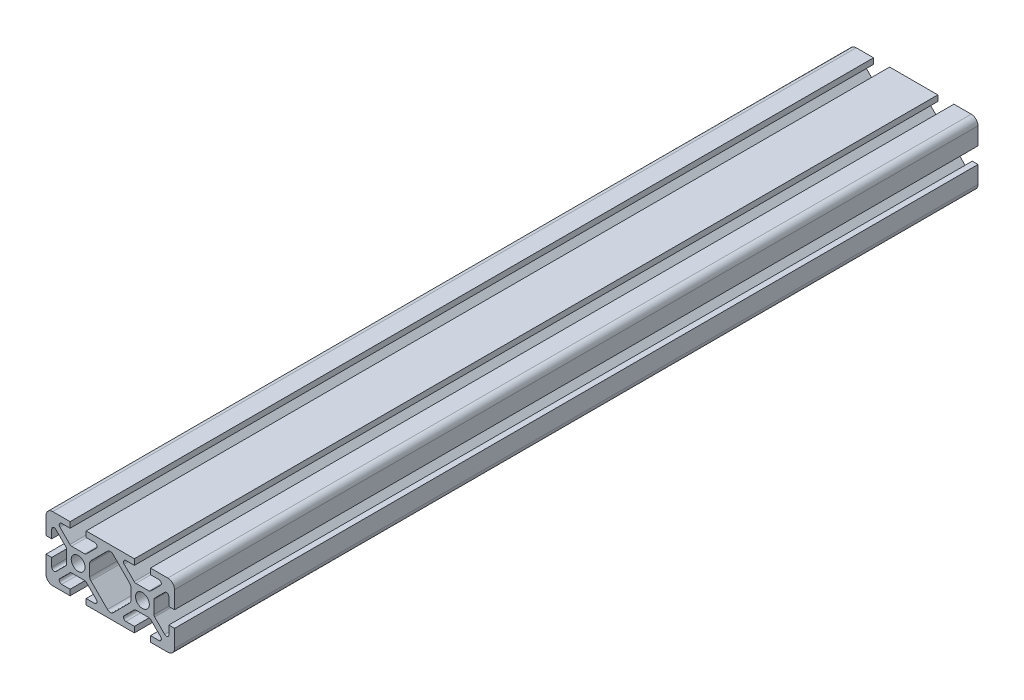
SolidWorks part; units mm, degrees
ref_plane "Front Plane" through (0, 0, 0) normal (0, 0, 1) x (1, 0, 0)
ref_plane "Top Plane" through (0, 0, 0) normal (0, 1, 0) x (1, 0, 0)
ref_plane "Right Plane" through (0, 0, 0) normal (1, 0, 0) x (0, 0, -1)
sketch "Sketch1" plane through (0, 0, 0) normal (0, 0, 1) x (1, 0, 0)
  line L0 (10, 10) -> (10, -10) construction
  line L1 (-20, 0) -> (20, 0) construction
  line L2 (12.5, -10) -> (20, -10)
  line L3 (20, -10) -> (20, -2.5)
  line L4 (12.5, -10) -> (12.5, -8.2134)
  line L5 (12.5, -8.2134) -> (16.95, -8.2134)
  line L6 (16.95, -8.2134) -> (12.3366, -3.6)
  line L7 (10, 0) -> (20, -10) construction
  line L8 (20, -2.5) -> (18.2134, -2.5)
  line L9 (18.2134, -2.5) -> (18.2134, -6.95)
  line L10 (18.2134, -6.95) -> (13.6, -2.3366)
  line L11 (15.9067, -4.6433) -> (14.6433, -5.9067) construction
  line L12 (0, 10) -> (0, -10) construction
  line L13 (0, -10) -> (-20, -10) construction
  line L14 (-10, 10) -> (10, 10) construction
  line L15 (20, 2.5) -> (20, -2.5) construction
  circle A0 centre (10, 0) radius 2.15
  arc A1 (15.5015, -8.2134) -> (15.9257, -7.1891) centre (15.5015, -7.6134) ccw construction
  point P8 (10, -3.6)
  point P16 (15.275, -5.275)
  point P30 (20, 0)
  dimension "Center Hole Diameter" = 4.3
  dimension "D3" = 0.6
  dimension "Rail Width" = 20
  dimension "T-Slot Width" = 5
  dimension "Slot Depth" = 6.4
  dimension "Rail Height" = 40
  dimension "Inner Slot Width" = 13.9
  dimension "Hole Spacing" = 20
sketch "Sketch2" plane through (0, 0, 0) normal (1, 0, 0) x (0, 0, -1)
  line L0 (-125, -10) -> (125, -10) construction
  line L1 (-85, 0) -> (85, 0) construction
  point P6 (-85, 0)
  point P8 (85, 0)
  dimension "Length" = 250
  dimension "D1" = 40
sketch "Sketch3" plane through (0, 0, 0) normal (0, 0, 1) x (1, 0, 0)
  line L0 (12.5, -10) -> (17.9, -10)
  line L1 (12.5, -10) -> (20, -10) construction
  line L2 (12.5, -10) -> (12.5, -8.2134) construction
  line L3 (12.5, -8.2134) -> (16.95, -8.2134) construction
  line L4 (12.5, -8.2134) -> (12.5, -10)
  line L5 (12.5, -8.2134) -> (16.95, -8.2134)
  line L6 (10, -3.6) -> (12.3366, -3.6)
  line L7 (16.95, -8.2134) -> (12.3366, -3.6) construction
  line L8 (12.3366, -3.6) -> (16.95, -8.2134)
  line L9 (20, -10) -> (20, -2.5) construction
  line L10 (18.2134, -6.95) -> (13.6, -2.3366) construction
  line L11 (18.2134, -2.5) -> (18.2134, -6.95) construction
  line L12 (18.2134, -6.95) -> (18.2134, -2.5)
  line L13 (20, -2.5) -> (18.2134, -2.5) construction
  line L14 (18.2134, -2.5) -> (20, -2.5)
  line L15 (20, -2.5) -> (20, -7.9)
  line L16 (18.2134, -6.95) -> (13.6, -2.3366)
  line L17 (13.6, 0) -> (13.6, -2.3366)
  line L18 (-20, 0) -> (20, 0) construction
  line L19 (10, -3.6) -> (10, -2.15)
  line L20 (10, 10) -> (10, -10) construction
  line L21 (13.6, 0) -> (12.15, 0)
  arc A5 (17.9, -10) -> (20, -7.9) centre (17.9, -7.9) ccw
  circle A10 centre (10, 0) radius 2.15 construction
  arc A11 (10, -2.15) -> (12.15, 0) centre (10, 0) ccw
  dimension "D1" = 2.1
extrude "Boss-Extrude1" add sketch "Sketch3" along normal mid plane 250
sketch "Sketch4" plane through (0, 0, 0) normal (0, 0, 1) x (1, 0, 0)
  line L0 (10, -3.6) -> (7.6634, -3.6)
  line L4 (7.6634, -3.6) -> (3.05, -8.2134)
  line L5 (3.05, -8.2134) -> (7.5, -8.2134)
  line L6 (7.5, -8.2134) -> (7.5, -10)
  line L18 (7.5, -10) -> (0, -10)
  line L19 (12.5, -10) -> (12.5, -8.2134) construction
  line L20 (12.5, -8.2134) -> (16.95, -8.2134) construction
  line L21 (10, -3.6) -> (12.3366, -3.6) construction
  line L22 (16.95, -8.2134) -> (12.3366, -3.6) construction
  line L23 (0, -8.7366) -> (6.4, -2.3366)
  line L24 (0, 10) -> (0, -10) construction
  line L25 (6.4, -2.3366) -> (6.4, 0)
  line L26 (-20, 0) -> (20, 0) construction
  line L27 (6.4, 0) -> (7.85, 0)
  line L28 (13.6, 0) -> (12.15, 0) construction
  line L29 (0, -8.7366) -> (0, -10)
  line L30 (10, -2.15) -> (10, -3.6)
  circle A4 centre (10, 0) radius 2.15 construction
  arc A5 (7.85, 0) -> (10, -2.15) centre (10, 0) ccw
extrude "Boss-Extrude2" add sketch "Sketch4" along normal mid plane 250
mirror "Mirror1" about plane through (0, 0, 0) normal (1, 0, 0) of bodies 137 134
mirror "Mirror2" about plane through (0, 0, 0) normal (0, 1, 0) of bodies 135
fillet "Fillet1" radius 0.75 24 edges at (-7.6634, -3.6, 0) (-12.3366, -3.6, 0) (12.3366, -3.6, 0) (7.6634, -3.6, 0) (-3.05, -8.2134, 0) (-18.2134, -6.95, 0) (-16.95, -8.2134, 0) (-13.6, -2.3366, 0) (-18.2134, 6.95, 0) (-16.95, 8.2134, 0) (-12.3366, 3.6, 0) (-7.6634, 3.6, 0) (-13.6, 2.3366, 0) (-3.05, 8.2134, 0) (3.05, 8.2134, 0) (13.6, -2.3366, 0) (18.2134, 6.95, 0) (13.6, 2.3366, 0) (7.6634, 3.6, 0) (12.3366, 3.6, 0) (16.95, 8.2134, 0) (18.2134, -6.95, 0) (16.95, -8.2134, 0) (3.05, -8.2134, 0)
fillet "Fillet2" radius 1.25 6 edges at (0, -8.7366, 0) (-6.4, -2.3366, 0) (-6.4, 2.3366, 0) (6.4, -2.3366, 0) (6.4, 2.3366, 0) (0, 8.7366, 0)
equation "\"D1@Sketch3\" = \"D3@Sketch1\" * 3.5"
equation "\"D1@Boss-Extrude1\" = \"Length@Sketch2\""
equation "\"D1@Boss-Extrude2\" = \"Length@Sketch2\""
equation "\"D1@Sketch2\"=\"Rail Height@Sketch1\""
